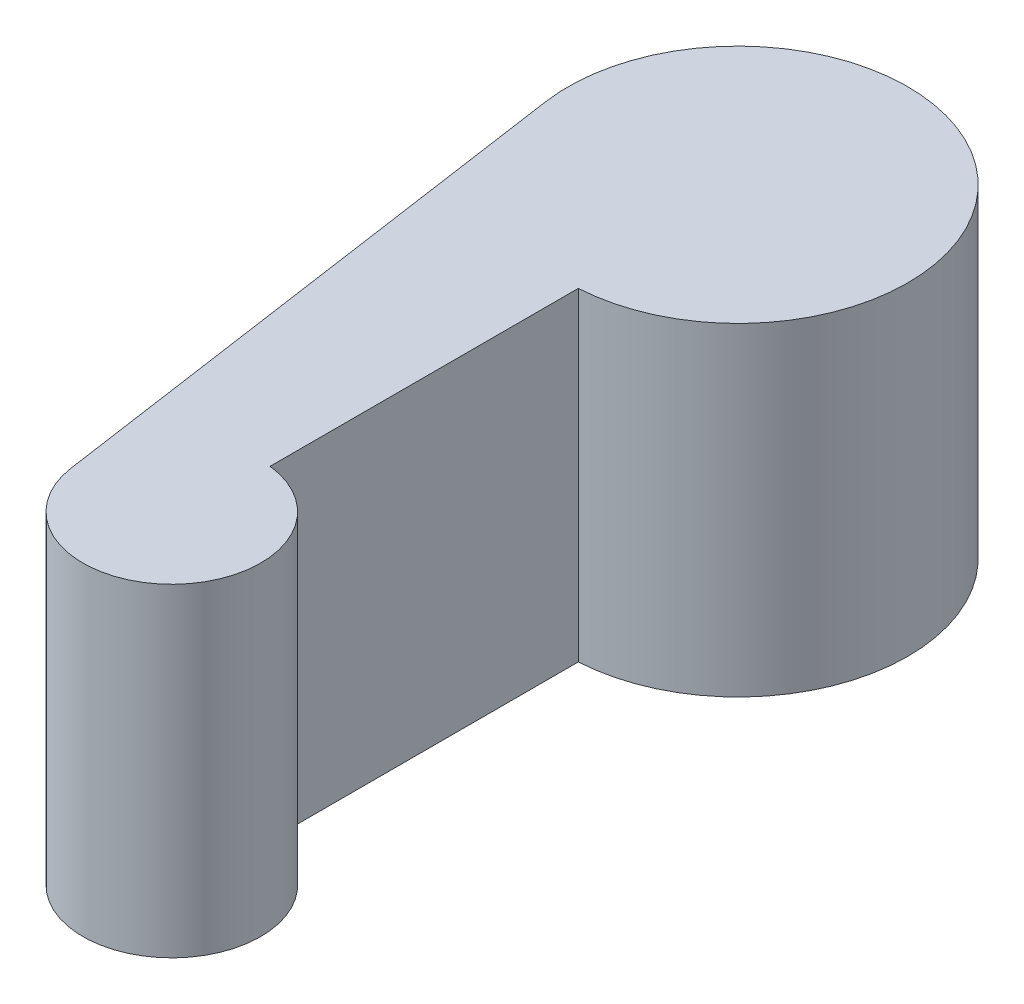
SolidWorks part; units mm, degrees
ref_plane "Front Plane" through (0, 0, 0) normal (0, 0, 1) x (1, 0, 0)
ref_plane "Top Plane" through (0, 0, 0) normal (0, 1, 0) x (1, 0, 0)
ref_plane "Right Plane" through (0, 0, 0) normal (1, 0, 0) x (0, 0, -1)
sketch "Sketch1" plane through (0, 0, 0) normal (0, 1, 0) x (1, 0, 0)
  line L0 (-0.5174, -19.0766) -> (-0.5174, -35.3971)
  line L1 (-0.5174, -35.3971) -> (-0.5174, 2.7062)
  line L2 (-17.5733, -13.6149) -> (-12.6246, -47.9007)
  line L3 (-12.6246, -47.9007) -> (-22.522, 20.6708)
  circle A0 centre (-1.7374, 23.6708) radius 21
  circle A1 centre (-1.7374, -46.3292) radius 11
extrude "Boss-Extrude1" add sketch "Sketch1" along normal blind 40 contours A0 | A1 L0 L1 A0 L3 L2 | A1 L3
